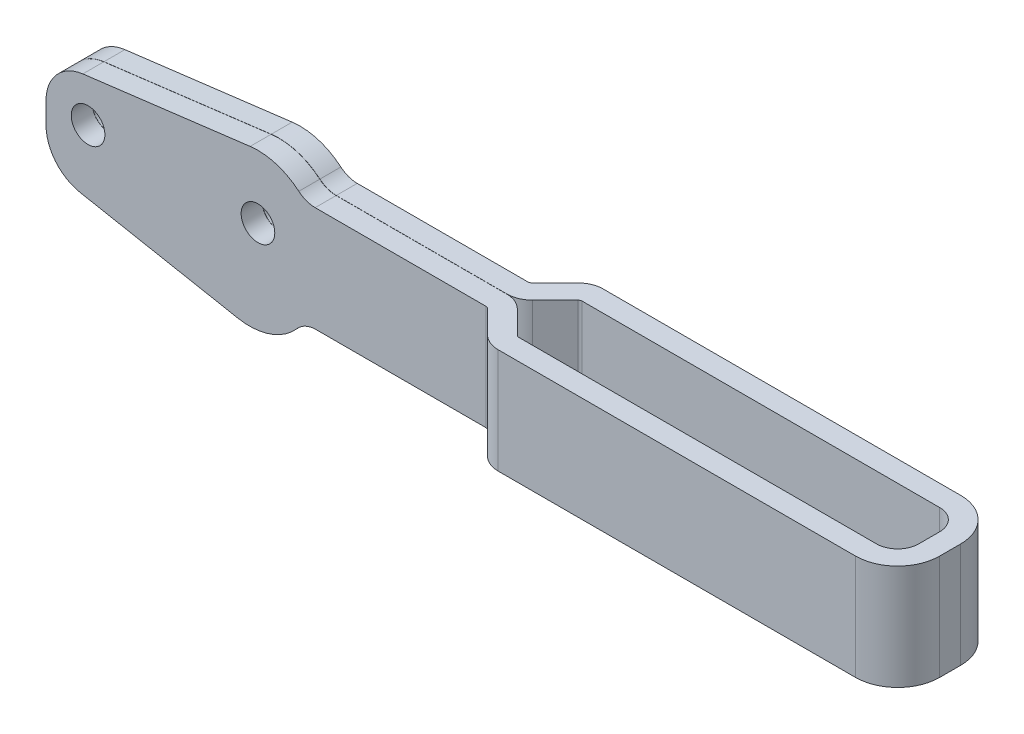
SolidWorks part; units mm, degrees
material "Plain Carbon Steel"
ref_plane "Plane1" through (0, 0, 0) normal (0, 0, 1) x (1, 0, 0)
ref_plane "Plane2" through (0, 0, 0) normal (0, 1, 0) x (-1, 0, 0)
ref_plane "Plane3" through (0, 0, 0) normal (1, 0, 0) x (0, 0, -1)
sketch "Sketch1" plane through (0, 0, 0) normal (0, 0, 1) x (1, 0, 0)
  line L0 (0, 0) -> (133.35, 0)
  line L1 (0, 0) -> (0, 15.875)
  line L2 (133.35, 15.875) -> (0, 15.875)
  line L3 (133.35, 15.875) -> (133.35, 0)
  dimension "D1" = 133.35
  dimension "D2" = 15.875
extrude "Base-Extrude" add sketch "Sketch1" along normal mid plane 15.875
sketch "Sketch3" plane through (0, 15.875, 0) normal (0, 1, 0) x (-1, 0, 0)
  line L0 (-72.7526, -4.7625) -> (-130.175, -4.7625)
  line L1 (0, 0) -> (-68.2806, 0) construction
  line L2 (-130.175, 4.7625) -> (-72.7526, 4.7625)
  line L3 (-130.175, 4.7625) -> (-130.175, -4.7625)
  line L4 (-133.35, -7.9375) -> (0, -7.9375) construction
  line L5 (-133.35, 7.9375) -> (-133.35, -7.9375) construction
  line L6 (-133.35, 7.9375) -> (0, 7.9375) construction
  line L7 (1.2474, -3.175) -> (-66.675, -3.175)
  line L8 (-72.7526, -4.7625) -> (-67.9901, 0)
  line L9 (-67.9901, 0) -> (-72.7526, 4.7625)
  line L10 (1.2474, 3.175) -> (-66.675, 3.175)
  line L11 (-66.675, -3.175) -> (-73.3711, -9.8711)
  line L12 (-66.675, 3.175) -> (-73.3711, 9.8711)
  line L13 (-73.3711, -9.8711) -> (1.2474, -9.8711)
  line L14 (-73.3711, 9.8711) -> (1.2474, 9.8711)
  line L15 (1.2474, -9.8711) -> (1.2474, -3.175)
  line L16 (1.2474, 9.8711) -> (1.2474, 3.175)
  point P19 (-66.675, 7.9375)
  dimension "D2" = 3.175
  dimension "D3" = 3.175
  dimension "D4" = 3.175
  dimension "D5" = 45
  dimension "D6" = 3.175
  dimension "D7" = 3.175
extrude "Cut-Extrude1" cut sketch "Sketch3" against normal through all
fillet "Fillet5" radius 0.635 4 edges at (72.7526, 7.9375, -4.7625) (72.7526, 7.9375, 4.7625) (66.675, 7.9375, 3.175) (66.675, 7.9375, -3.175)
fillet "Fillet6" radius 3.81 2 edges at (71.4375, 7.9375, 7.9375) (71.4375, 7.9375, -7.9375)
fillet "Fillet7" radius 3.175 2 edges at (130.175, 7.9375, -4.7625) (130.175, 7.9375, 4.7625)
fillet "Fillet8" radius 6.35 2 edges at (133.35, 7.9375, 7.9375) (133.35, 7.9375, -7.9375)
fillet "Fillet9" radius 6.35 1 edges at (0, 15.875, 0)
fillet "Fillet10" radius 6.35 1 edges at (0, 0, 0)
sketch "Sketch6" plane through (0, 0, 3.175) normal (0, 0, 1) x (1, 0, 0)
  line L0 (6.35, 15.875) -> (66.412, 15.875) construction
  line L1 (7.6318, 9.525) -> (42.545, 9.525) construction
  line L2 (0, 6.35) -> (0, 9.525) construction
  line L3 (76.2, 36.1043) -> (76.2, -14.5143) construction
  line L4 (133.35, 15.875) -> (133.35, 0) construction
  line L5 (5.5641, 15.8262) -> (30.8252, 18.9768)
  line L7 (29.4622, 19.05) -> (53.4108, 19.05) construction
  line L8 (28.2376, -4.572) -> (39.9397, -4.572) construction
  line L9 (5.1654, 0.1115) -> (28.9491, -4.4048)
  line L10 (0, 6.35) -> (0, 9.525)
  arc A0 (6.35, 15.875) -> (0, 9.525) centre (6.35, 9.525) ccw construction
  arc A2 (40.249, 4.7558) -> (30.8252, 18.9768) centre (32.004, 9.525) ccw
  arc A3 (5.5641, 15.8262) -> (0, 9.525) centre (6.35, 9.525) ccw
  arc A4 (40.249, 4.7558) -> (28.9491, -4.4048) centre (30.7261, 4.953) cw
  arc A5 (0, 6.35) -> (6.35, 0) centre (6.35, 6.35) ccw construction
  arc A6 (0, 6.35) -> (5.1654, 0.1115) centre (6.35, 6.35) ccw
  dimension "D1" = 19.05
  dimension "D4" = 24.4161
  dimension "D5" = 9.525
  dimension "D2" = 57.15
  dimension "D3" = 25.654
  dimension "D6" = 23.622
  dimension "D7" = 6.35
extrude "Boss-Extrude3" add sketch "Sketch6" against normal up to surface (6.35 mm away)
fillet "Fillet11" radius 3.81 2 edges at (38.862, 0, 0) (39.1035, 15.875, 0)
sketch "Sketch7" plane through (0, 0, 3.175) normal (0, 0, 1) x (1, 0, 0)
  circle A0 centre (6.35, 9.525) radius 2.54
  circle A1 centre (32.004, 9.525) radius 2.54
  arc A2 (5.5641, 15.8262) -> (0, 9.525) centre (6.35, 9.525) ccw construction
  arc A3 (38.1732, 16.7821) -> (30.8252, 18.9768) centre (32.004, 9.525) ccw construction
  dimension "D1" = 5.08
extrude "Cut-Extrude5" cut sketch "Sketch7" against normal through all
sketch "Sketch8" plane through (0, 15.875, 0) normal (0, 1, 0) x (-1, 0, 0)
  line L0 (0, 0) -> (-59.8442, 0) construction
  line L1 (-73.0157, -4.7625) -> (-73.0157, 5.9871) construction
  line L2 (3.175, 0.0127) -> (-73.0157, 0.0127)
  line L3 (3.175, 0.0127) -> (3.175, -0.0127)
  line L4 (-73.0157, -0.0127) -> (3.175, -0.0127)
  line L5 (-73.0157, -0.0127) -> (-73.0157, 0.0127)
  line L6 (0, 3.175) -> (0, -3.175) construction
  dimension "D1" = 3.175
  dimension "D2" = 0.0127
  dimension "D3" = 0.0254
extrude "Cut-Extrude6" cut sketch "Sketch8" against normal through all and the other way through all
fillet "Fillet12" radius 3.81 1 edges at (68.0028, 7.9375, 0.0127)
fillet "Fillet13" radius 3.81 1 edges at (68.0028, 7.9375, -0.0127)
equation "\"D2@Sketch3\" = \"D3@Sketch3\""
equation "\"D4@Sketch3\" = \"D2@Sketch3\""
equation "\"D6@Sketch3\" = \"D2@Sketch3\""
equation "\"D7@Sketch3\" = \"D2@Sketch3\""
